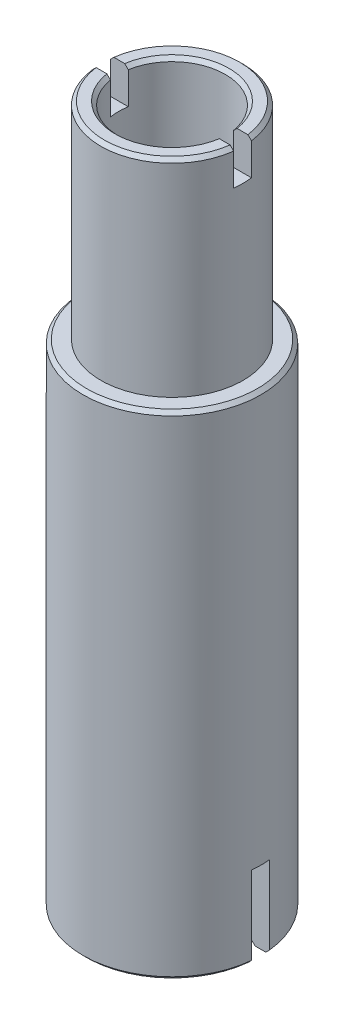
SolidWorks part; units mm, degrees
material "PA Type 6"
ref_plane "Front Plane" through (0, 0, 0) normal (0, 0, 1) x (1, 0, 0)
ref_plane "Top Plane" through (0, 0, 0) normal (0, 1, 0) x (1, 0, 0)
ref_plane "Right Plane" through (0, 0, 0) normal (1, 0, 0) x (0, 0, -1)
sketch "Sketch1" plane through (0, 0, 0) normal (0, 0, 1) x (1, 0, 0)
  line L0 (0, 0) -> (0, 27.3374) construction
  line L1 (20, -138.5) -> (25, -138.5)
  line L2 (25, -138.5) -> (25, 0)
  line L3 (25, 0) -> (20, 0)
  line L4 (20, 0) -> (20, 58)
  line L5 (20, 58) -> (15, 58)
  line L6 (15, 58) -> (15, -50)
  line L7 (15, -50) -> (20, -50)
  line L9 (20, -50) -> (20, -138.5)
  dimension "D1" = 5
  dimension "D2" = 138.5
  dimension "D3" = 58
  dimension "D4" = 5
  dimension "D6" = 25
  dimension "D7" = 15
  dimension "D8" = 50
revolve "Revolve1" add sketch "Sketch1" angle 360 about L0
sketch "Sketch2" plane through (0, 58, 0) normal (0, 1, 0) x (1, 0, 0)
  line L1 (-27.5, -2.5) -> (27.5, -2.5)
  line L2 (-27.5, -2.5) -> (-27.5, 2.5)
  line L3 (-27.5, 2.5) -> (27.5, 2.5)
  line L4 (27.5, -2.5) -> (27.5, 2.5)
  line L5 (-27.5, -2.5) -> (27.5, 2.5) construction
  line L6 (-27.5, 2.5) -> (27.5, -2.5) construction
  point P0 (0, 0)
  dimension "D1" = 5
  dimension "D2" = 55
extrude "Cut-Extrude1" cut sketch "Sketch2" against normal blind 10
sketch "Sketch3" plane through (0, -138.5, 0) normal (0, -1, 0) x (-1, 0, 0)
  line L1 (35, -2.5) -> (-35, -2.5)
  line L2 (35, -2.5) -> (35, 2.5)
  line L3 (35, 2.5) -> (-35, 2.5)
  line L4 (-35, -2.5) -> (-35, 2.5)
  line L5 (35, -2.5) -> (-35, 2.5) construction
  line L6 (35, 2.5) -> (-35, -2.5) construction
  point P0 (0, 0)
  dimension "D1" = 5
  dimension "D2" = 70
extrude "Cut-Extrude2" cut sketch "Sketch3" against normal blind 23
chamfer "Chamfer1" distance 1 angle 45 10 edges at (0, 0, -25) (0, -138.5, -20) (0, -138.5, -25) (0, -138.5, 20) (0, -138.5, 25) (0, 58, -20) (0, 58, -15) (0, 58, 20) (0, 58, 15) (0, -50, -15)
